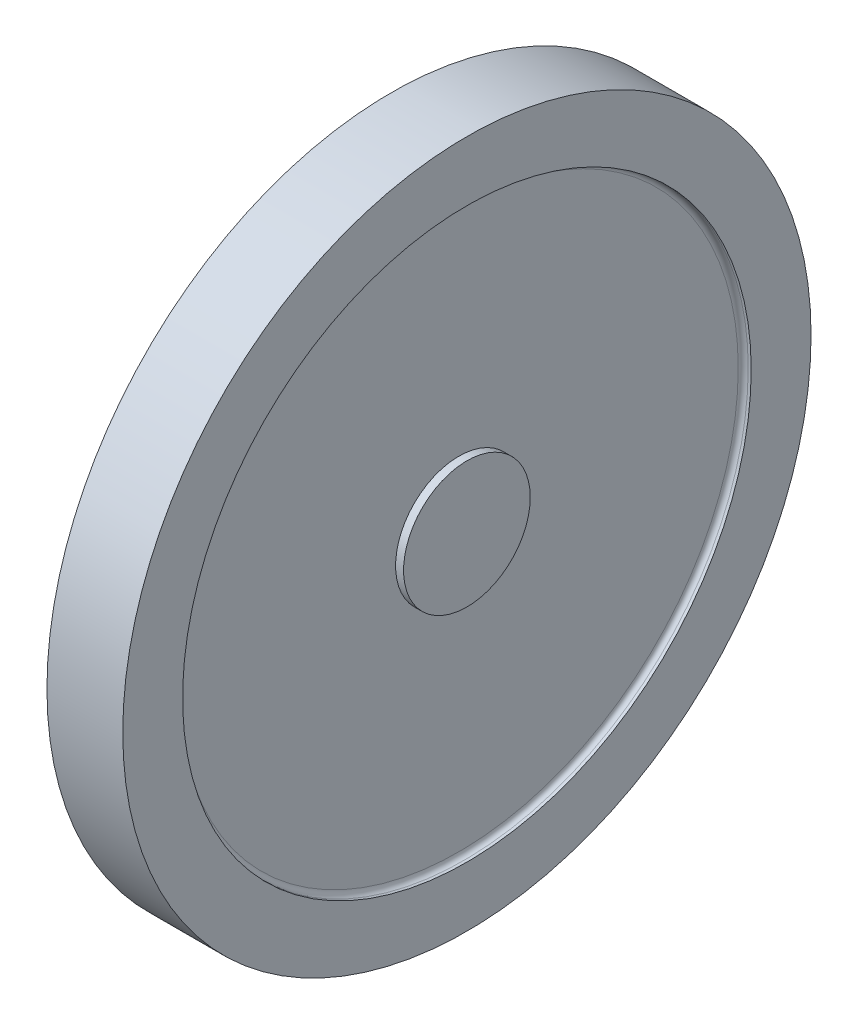
SolidWorks part; units mm, degrees
ref_plane "Front Plane" through (0, 0, 0) normal (0, 0, 1) x (1, 0, 0)
ref_plane "Top Plane" through (0, 0, 0) normal (0, 1, 0) x (1, 0, 0)
ref_plane "Right Plane" through (0, 0, 0) normal (1, 0, 0) x (0, 0, -1)
sketch "Sketch3" plane through (0, 0, 0) normal (0, 0, 1) x (1, 0, 0)
  line L0 (-7.6, 28.5) -> (-6.8, 28.5)
  line L1 (-0.8, 0) -> (-6.8, 0)
  line L2 (0, 28.5) -> (0, 34.5)
  line L3 (0, 34.5) -> (-7.6, 34.5)
  line L4 (-7.6, 28.5) -> (-7.6, 34.5)
  line L5 (-3.8, 28.5) -> (-3.8, 0) construction
  line L6 (-6.8, 28.5) -> (-6.8, 0)
  line L7 (-0.8, 28.5) -> (-0.8, 6.35)
  line L8 (-0.8, 28.5) -> (0, 28.5)
  line L10 (-0.8, 6.35) -> (0, 6.35)
  line L12 (-0.8, 0) -> (0, 0)
  line L13 (0, 6.35) -> (0, 0)
  dimension "D1" = 6.35
  dimension "D2" = 7.6
  dimension "D3" = 6
  dimension "D4" = 3
revolve "Revolve1" add sketch "Sketch3" angle 360 about L1
fillet "Fillet1" radius 0.5 2 edges at (-6.8, 0, -28.5) (-0.8, 0, -28.5)
